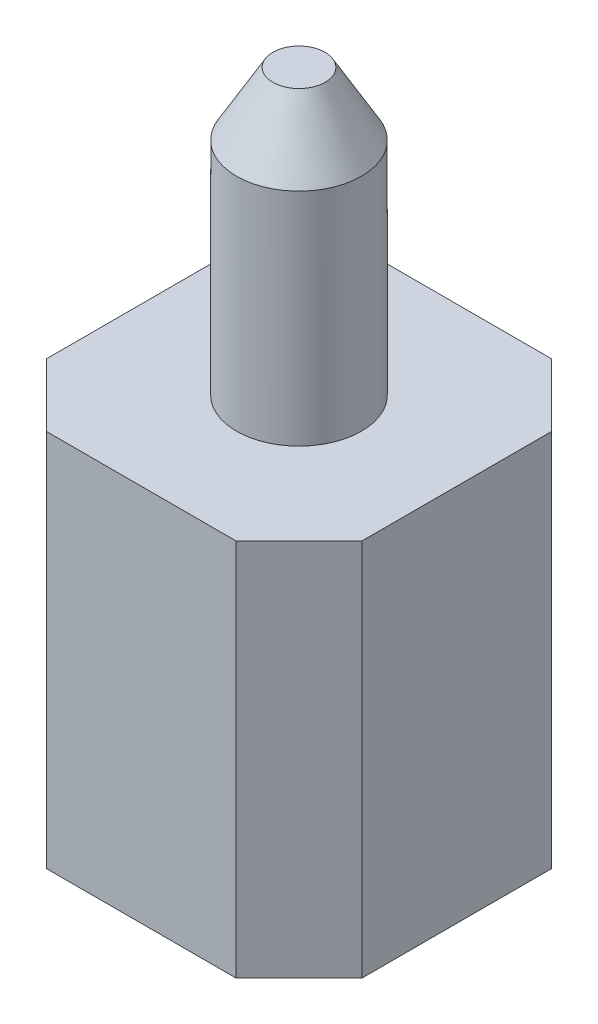
SolidWorks part; units mm, degrees
ref_plane "Front Plane" through (0, 0, 0) normal (0, 0, 1) x (1, 0, 0)
ref_plane "Top Plane" through (0, 0, 0) normal (0, 1, 0) x (1, 0, 0)
ref_plane "Right Plane" through (0, 0, 0) normal (1, 0, 0) x (0, 0, -1)
sketch "Sketch1" plane through (0, 0, 0) normal (0, 1, 0) x (1, 0, 0)
  line L0 (0, 0) -> (0, 69.6893) construction
  line L1 (0, 0) -> (68.5311, 0) construction
  line L2 (-1.25, 1.25) -> (1.25, 1.25)
  line L3 (1.25, 1.25) -> (1.25, -1.25)
  line L4 (-1.25, 1.25) -> (-1.25, -1.25)
  line L5 (-1.25, -1.25) -> (1.25, -1.25)
  point P8 (0, 1.25)
  point P10 (-1.25, 0)
  point P11 (1.25, 0)
  dimension "D1" = 2.5
extrude "Boss-Extrude1" add sketch "Sketch1" along normal mid plane 3
sketch "Sketch2" plane through (0, 1.5, 0) normal (0, 1, 0) x (1, 0, 0)
  line L0 (0, 1.25) -> (0, -1.25) construction
  line L1 (1.25, 0) -> (-1.25, 0) construction
  line L4 (-1.25, -1.25) -> (1.25, -1.25)
  line L5 (1.25, -1.25) -> (1.25, 1.25)
  line L6 (1.25, 1.25) -> (-1.25, 1.25)
  line L7 (-1.25, 1.25) -> (-1.25, -1.25)
  line L8 (-1.25, -1.25) -> (1.25, -1.25)
  line L9 (1.25, -1.25) -> (1.25, 1.25)
  line L10 (1.25, 1.25) -> (-1.25, 1.25)
  line L11 (-1.25, 1.25) -> (-1.25, -1.25)
  circle A0 centre (0, 0) radius 0.4953
  dimension "D2" = 0.9906
  dimension "D1" = 0
extrude "Boss-Extrude2" add sketch "Sketch2" along normal blind 2.25 contours A0
chamfer "Chamfer1" distance 0.5 angle 30 1 edges at (0, 3.75, 0.4953)
chamfer "Chamfer2" distance 0.5 angle 45 4 edges at (-1.25, 0, -1.25) (1.25, 0, -1.25) (1.25, 0, 1.25) (-1.25, 0, 1.25)
